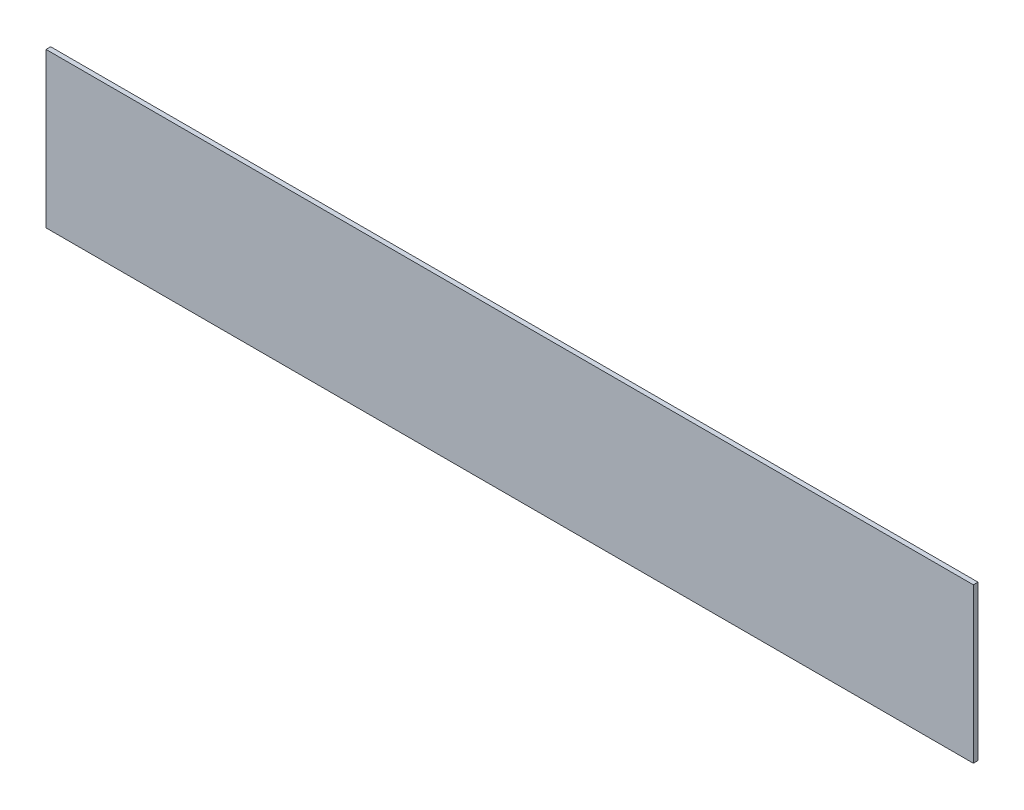
SolidWorks part; units mm, degrees
material "PMMA"
ref_plane "Front Plane" through (0, 0, 0) normal (0, 0, 1) x (1, 0, 0)
ref_plane "Top Plane" through (0, 0, 0) normal (0, 1, 0) x (1, 0, 0)
ref_plane "Right Plane" through (0, 0, 0) normal (1, 0, 0) x (0, 0, -1)
sketch "Sketch1" plane through (0, 0, 0) normal (0, 0, 1) x (1, 0, 0)
  line L1 (0, 0) -> (600, 0)
  line L2 (0, 0) -> (0, 100)
  line L3 (0, 100) -> (600, 100)
  line L4 (600, 0) -> (600, 100)
  dimension "D1" = 600
  dimension "D2" = 100
extrude "Boss-Extrude1" add sketch "Sketch1" along normal blind 3
